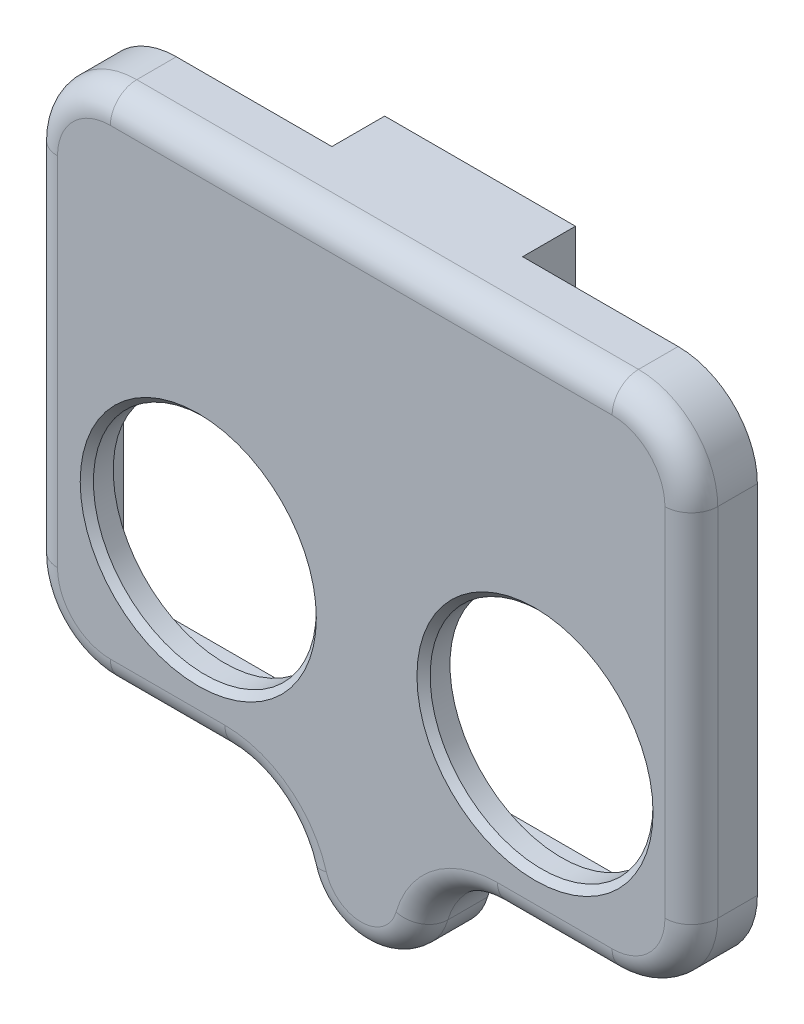
SolidWorks part; units mm, degrees
ref_plane "Front Plane" through (0, 0, 0) normal (0, 0, 1) x (1, 0, 0)
ref_plane "Top Plane" through (0, 0, 0) normal (0, 1, 0) x (1, 0, 0)
ref_plane "Right Plane" through (0, 0, 0) normal (1, 0, 0) x (0, 0, -1)
sketch "Sketch1" plane through (0, 0, 0) normal (0, 0, 1) x (1, 0, 0)
  line L0 (0, 0) -> (0, -37) construction
  line L38 (6.723, -16) -> (23, -16)
  line L39 (6.723, -16) -> (23, -16)
  line L40 (23, -16) -> (23, -37)
  line L41 (23, -16) -> (23, -37)
  line L42 (23, -37) -> (-23, -37)
  line L43 (23, -37) -> (-23, -37)
  line L44 (-23, -37) -> (-23, -16)
  line L45 (-23, -37) -> (-23, -16)
  line L46 (-23, -16) -> (-6.723, -16)
  line L47 (-23, -16) -> (6.723, -16)
  line L55 (19, 0) -> (7.723, 0)
  line L56 (7.723, 0) -> (7.723, -6.1725)
  line L57 (7.723, -6.1725) -> (6.723, -7.1725)
  line L58 (6.723, -7.1725) -> (6.723, -16)
  line L64 (-6.723, -16) -> (-6.723, -7.1725)
  line L65 (-6.723, -7.1725) -> (-7.723, -6.1725)
  line L66 (-7.723, -6.1725) -> (-7.723, 0)
  line L67 (-7.723, 0) -> (-19, 0)
  line L72 (-25, -6) -> (-25, -33)
  line L73 (-19, -39) -> (-10.3229, -39)
  line L76 (10.3229, -39) -> (19, -39)
  line L77 (25, -33) -> (25, -6)
  line L82 (19, 0) -> (7.723, 0)
  line L94 (7.723, 0) -> (-19, 0)
  line L99 (-25, -6) -> (-25, -33)
  line L100 (-19, -39) -> (-10.3229, -39)
  line L103 (10.3229, -39) -> (19, -39)
  line L104 (25, -33) -> (25, -6)
  circle A1 centre (-20, -5) radius 1.5
  circle A2 centre (0, -42) radius 1.5
  circle A3 centre (0, -42) radius 1.75 construction
  circle A5 centre (-20, -5) radius 1.75 construction
  arc A6 (25, -6) -> (19, 0) centre (19, -6) ccw
  arc A7 (-4.5613, -43.3256) -> (4.5613, -43.3256) centre (0, -42) ccw
  arc A8 (25, -6) -> (19, 0) centre (19, -6) ccw
  arc A10 (-4.5613, -43.3256) -> (4.5613, -43.3256) centre (0, -42) ccw
  circle A12 centre (0, -42) radius 1.75 construction
  circle A14 centre (-20, -5) radius 1.75 construction
  circle A15 centre (20, -5) radius 1.5
  arc A29 (-19, 0) -> (-25, -6) centre (-19, -6) ccw
  arc A30 (-19, 0) -> (-25, -6) centre (-19, -6) ccw
  arc A43 (-25, -33) -> (-19, -39) centre (-19, -33) ccw
  arc A44 (-25, -33) -> (-19, -39) centre (-19, -33) ccw
  arc A45 (-4.5613, -43.3256) -> (-10.3229, -39) centre (-10.3229, -45) ccw
  arc A46 (-4.5613, -43.3256) -> (-10.3229, -39) centre (-10.3229, -45) ccw
  arc A47 (10.3229, -39) -> (4.5613, -43.3256) centre (10.3229, -45) ccw
  arc A48 (10.3229, -39) -> (4.5613, -43.3256) centre (10.3229, -45) ccw
  arc A49 (19, -39) -> (25, -33) centre (19, -33) ccw
  arc A50 (19, -39) -> (25, -33) centre (19, -33) ccw
  dimension "D2" = 3
  dimension "D1" = 0
extrude "Boss-Extrude1" add sketch "Sketch1" along normal blind 3
sketch "Sketch3" plane through (0, 0, 0) normal (0, 0, -1) x (-1, 0, 0)
  line L0 (6.723, -7.1725) -> (6.723, -17.5725) construction
  line L1 (-7.223, 0) -> (-7.223, -5.9654)
  line L2 (-7.223, -5.9654) -> (-6.223, -6.9654)
  line L3 (-6.223, -6.9654) -> (-6.223, -10.0445)
  line L4 (-6.223, -10.0445) -> (6.223, -10.0445)
  line L5 (6.223, -10.0445) -> (6.223, -6.9654)
  line L6 (6.223, -6.9654) -> (7.223, -5.9654)
  line L7 (7.223, -5.9654) -> (7.223, 0)
  line L8 (-7.223, 0) -> (7.223, 0)
  line L12 (5.4638, -10.5445) -> (5.4638, -17.5725)
  line L13 (-5.4638, -10.5445) -> (5.4638, -10.5445)
  line L14 (-5.4638, -17.5725) -> (-5.4638, -10.5445)
  line L15 (-6.723, -17.5725) -> (-5.4638, -17.5725)
  line L16 (-6.723, -7.1725) -> (-6.723, -17.5725)
  line L17 (-7.723, -6.1725) -> (-6.723, -7.1725)
  line L18 (-7.723, 0) -> (-7.723, -6.1725)
  line L19 (7.723, 0) -> (-7.723, 0)
  line L20 (7.723, -6.1725) -> (7.723, 0)
  line L21 (6.723, -7.1725) -> (7.723, -6.1725)
  line L22 (6.723, -17.5725) -> (6.723, -7.1725)
  line L23 (5.4638, -17.5725) -> (6.723, -17.5725)
  line L25 (-6.723, -10.5445) -> (6.723, -10.5445) construction
  line L28 (-6.723, -7.1725) -> (-6.723, -10.5445) construction
  line L29 (-7.723, -6.1725) -> (-6.723, -7.1725) construction
  line L30 (-7.723, 0) -> (-7.723, -6.1725) construction
  line L31 (7.723, 0) -> (-7.723, 0)
  line L32 (7.723, -6.1725) -> (7.723, 0) construction
  line L33 (6.723, -7.1725) -> (7.723, -6.1725) construction
  line L34 (6.723, -10.5445) -> (6.723, -7.1725) construction
  dimension "D1" = 0
  dimension "D2" = 0.5
extrude "Boss-Extrude2" add sketch "Sketch3" along normal blind 4 contours L1 L2 L3 L4 L5 L6 L7 L8
sketch "Sketch5" plane through (0, 0, 3) normal (0, 0, 1) x (1, 0, 0)
  line L18 (19, 0) -> (-19, 0)
  line L23 (-25, -6) -> (-25, -33)
  line L24 (-19, -39) -> (-10.3229, -39)
  line L27 (10.3229, -39) -> (19, -39)
  line L28 (25, -33) -> (25, -6)
  line L33 (19, 0) -> (-19, 0)
  line L38 (-25, -6) -> (-25, -33)
  line L39 (-19, -39) -> (-10.3229, -39)
  line L42 (10.3229, -39) -> (19, -39)
  line L43 (25, -33) -> (25, -6)
  arc A3 (25, -6) -> (19, 0) centre (19, -6) ccw
  arc A4 (25, -6) -> (19, 0) centre (19, -6) ccw
  arc A5 (-4.5613, -43.3256) -> (4.5613, -43.3256) centre (0, -42) ccw
  arc A8 (-4.5613, -43.3256) -> (4.5613, -43.3256) centre (0, -42) ccw
  arc A13 (-19, 0) -> (-25, -6) centre (-19, -6) ccw
  circle A14 centre (13.16, -26.5) radius 8.44
  circle A15 centre (13.16, -26.5) radius 8.44
  arc A16 (-19, 0) -> (-25, -6) centre (-19, -6) ccw
  circle A17 centre (-12.34, -26.5) radius 8.44
  circle A18 centre (-12.34, -26.5) radius 8.44
  arc A1949 (-25, -33) -> (-19, -39) centre (-19, -33) ccw
  arc A1950 (-25, -33) -> (-19, -39) centre (-19, -33) ccw
  arc A1951 (-4.5613, -43.3256) -> (-10.3229, -39) centre (-10.3229, -45) ccw
  arc A1952 (-4.5613, -43.3256) -> (-10.3229, -39) centre (-10.3229, -45) ccw
  arc A1953 (10.3229, -39) -> (4.5613, -43.3256) centre (10.3229, -45) ccw
  arc A1954 (10.3229, -39) -> (4.5613, -43.3256) centre (10.3229, -45) ccw
  arc A1955 (19, -39) -> (25, -33) centre (19, -33) ccw
  arc A1956 (19, -39) -> (25, -33) centre (19, -33) ccw
  dimension "D1" = 0
  dimension "D2" = 0.5
  dimension "D3" = 0.5
extrude "Boss-Extrude3" add sketch "Sketch5" along normal blind 2
fillet "Fillet3" radius 2 12 edges at (0, 0, 5) (-25, -19.5, 5) (14.6615, -39, 5) (-14.6615, -39, 5) (0, -46.75, 5) (25, -19.5, 5) (-23.2426, -37.2426, 5) (-6.7206, -40.2017, 5) (6.7206, -40.2017, 5) (23.2426, -37.2426, 5) (-23.2426, -1.7574, 5) (23.2426, -1.7574, 5)
chamfer "Chamfer1" distance 0.5 angle 45 2 edges at (21.6, -26.5, 5) (-3.9, -26.5, 5)
